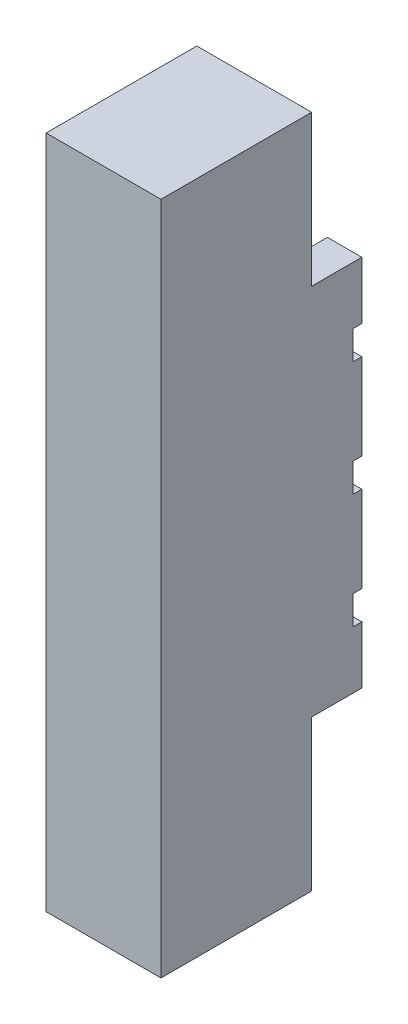
SolidWorks part; units mm, degrees
material "Alloy Steel"
ref_plane "Front Plane" through (0, 0, 0) normal (0, 0, 1) x (1, 0, 0)
ref_plane "Top Plane" through (0, 0, 0) normal (0, 1, 0) x (1, 0, 0)
ref_plane "Right Plane" through (0, 0, 0) normal (1, 0, 0) x (0, 0, -1)
sketch "Sketch1" plane through (0, 0, 0) normal (0, 1, 0) x (1, 0, 0)
  line L0 (0, 27.5) -> (0, 0) construction
  line L1 (-20, -35) -> (20, -35)
  line L2 (-20, -35) -> (-20, 35)
  line L3 (-20, 35) -> (20, 35)
  line L4 (20, -35) -> (20, 35)
  line L5 (-20, -35) -> (20, 35) construction
  line L6 (-20, 35) -> (20, -35) construction
  line L7 (-8, 35) -> (-8, 27.5)
  line L8 (-8, 27.5) -> (8, 27.5)
  line L9 (8, 27.5) -> (8, 35)
  point P0 (0, 0)
  dimension "D1" = 70
  dimension "D2" = 40
  dimension "D3" = 16
  dimension "D4" = 7.5
extrude "Boss-Extrude1" add sketch "Sketch1" along normal blind 130 contours L9 L8 L7 L3 L2 L1 L4
sketch "Sketch2" plane through (0, 0, -35) normal (0, 0, -1) x (-1, 0, 0)
  line L0 (0, 0) -> (0, 130) construction
  line L1 (8, 130) -> (-8, 130) construction
  line L2 (20, 65) -> (-20, 65) construction
  line L3 (-20, 130) -> (-20, 0) construction
  line L4 (20, 75) -> (-20, 75) construction
  line L5 (20, 85) -> (-20, 85) construction
  line L6 (20, 95) -> (-20, 95) construction
  line L7 (20, 105) -> (-20, 105) construction
  line L8 (20, 115) -> (-20, 115) construction
  line L9 (20, 55) -> (-20, 55) construction
  line L10 (20, 45) -> (-20, 45) construction
  line L11 (20, 35) -> (-20, 35) construction
  line L12 (20, 25) -> (-20, 25) construction
  line L13 (20, 15) -> (-20, 15) construction
  line L15 (20, 30) -> (-20, 30)
  line L16 (20, 30) -> (20, 20)
  line L17 (20, 20) -> (-20, 20)
  line L18 (-20, 30) -> (-20, 20)
  line L19 (20, 30) -> (-20, 20) construction
  line L20 (20, 20) -> (-20, 30) construction
  line L37 (20, 70) -> (-20, 70)
  line L38 (20, 70) -> (20, 60)
  line L39 (20, 60) -> (-20, 60)
  line L40 (-20, 70) -> (-20, 60)
  line L41 (20, 70) -> (-20, 60) construction
  line L42 (20, 60) -> (-20, 70) construction
  line L44 (20, 110) -> (-20, 110)
  line L45 (20, 110) -> (20, 100)
  line L46 (20, 100) -> (-20, 100)
  line L47 (-20, 110) -> (-20, 100)
  line L48 (20, 110) -> (-20, 100) construction
  line L49 (20, 100) -> (-20, 110) construction
  point P5 (0, 25)
  point P8 (0, 65)
  point P35 (0, 65)
  point P36 (0, 105)
  dimension "D3" = 10
  dimension "D4" = 40
  dimension "D5" = 10
  dimension "D6" = 10
  dimension "D7" = 10
  dimension "D8" = 40
  dimension "D9" = 40
  dimension "D10" = 10
  dimension "D1" = 6
  dimension "D2" = 6
extrude "Cut-Extrude1" cut sketch "Sketch2" against normal blind 3
sketch "Sketch3" plane through (0, 0, -32) normal (0, 0, -1) x (-1, 0, 0)
  line L0 (14, 20) -> (14, 110) construction
  line L1 (8, 20) -> (20, 20) construction
  line L3 (-14, 20) -> (-14, 110) construction
  line L4 (-20, 20) -> (-8, 20) construction
  line L6 (0, 0) -> (0, 130) construction
  line L7 (8, 130) -> (-8, 130) construction
  line L8 (-14, 20) -> (-14, 110) construction
  line L9 (20, 110) -> (8, 110) construction
  line L10 (-8, 110) -> (-20, 110) construction
  point P12 (14, 25)
  point P13 (14, 65)
  point P15 (14, 105)
  point P27 (-14, 105)
  point P28 (-14, 25)
  point P29 (-14, 65)
  dimension "D1" = 5
  dimension "D3" = 40
  dimension "D2" = 3
hole_wizard "M3 Tapped Hole1" positions "3DSketch2" profile "Sketch6" tap size "M3" standard "DIN"
sketch3d "3DSketch2"
  point P0 (-14, 25, -32)
  point P3 (14, 25, -32)
  point P12 (-14, 105, -32)
  point P15 (14, 105, -32)
  point P53 (-14, 65, -32)
  point P56 (14, 65, -32)
cosmetic thread "Cosmetic Thread1" parameters "D2"=3
cosmetic thread "Cosmetic Thread3" parameters "D2"=3
cosmetic thread "Cosmetic Thread4" parameters "D2"=3
cosmetic thread "Cosmetic Thread6" parameters "D2"=3
cosmetic thread "Cosmetic Thread7" parameters "D2"=3
cosmetic thread "Cosmetic Thread9" parameters "D2"=3
sketch "Sketch6" plane through (-14, 25, -32) normal (1, 0, 0) x (0, 1, 0)
  line L0 (0, 0) -> (0, 8.7511)
  line L1 (0, 8.7511) -> (1.25, 8)
  line L2 (1.25, 8) -> (1.25, 0)
  line L5 (1.25, 0) -> (0, 0)
  line L10 (0, 8.7511) -> (-1.25, 8) construction
  line L11 (0, -6.35) -> (0, 107.95) construction
  dimension "Tap Drill Dia." = 2.5
  dimension "Tap Drill Depth" = 8
  dimension "Drill Angle" = 118
sketch "Sketch7" plane through (0, 0, -27.5) normal (0, 0, -1) x (-1, 0, 0)
  line L0 (0, 0) -> (0, 130) construction
  line L1 (8, 0) -> (-8, 0) construction
  line L2 (8, 130) -> (-8, 130) construction
  line L3 (14, 25) -> (-14, 25) construction
  line L4 (-14, 65) -> (14, 65) construction
  line L5 (14, 105) -> (-14, 105) construction
  point P18 (0, 65)
  point P19 (0, 25)
  point P20 (0, 105)
hole_wizard "M3 Tapped Hole2" positions "3DSketch3" profile "Sketch8" tap size "M3" standard "DIN"
sketch3d "3DSketch3"
  point P0 (0, 25, -27.5)
  point P3 (0, 65, -27.5)
  point P6 (0, 105, -27.5)
cosmetic thread "Cosmetic Thread2" parameters "D2"=3
cosmetic thread "Cosmetic Thread5" parameters "D2"=3
cosmetic thread "Cosmetic Thread8" parameters "D2"=3
sketch "Sketch8" plane through (0, 25, -27.5) normal (1, 0, 0) x (0, 1, 0)
  line L0 (0, 0) -> (0, 8.7511)
  line L1 (0, 8.7511) -> (1.25, 8)
  line L2 (1.25, 8) -> (1.25, 0)
  line L5 (1.25, 0) -> (0, 0)
  line L10 (0, 8.7511) -> (-1.25, 8) construction
  line L11 (0, -6.35) -> (0, 107.95) construction
  dimension "Tap Drill Dia." = 2.5
  dimension "Tap Drill Depth" = 8
  dimension "Drill Angle" = 118
sketch "Sketch9" plane through (-20, 0, 0) normal (-1, 0, 0) x (0, 0, 1)
  line L1 (-17.5, -52.5) -> (-17.5, 0)
  line L2 (35, 0) -> (-35, 0) construction
  line L3 (35, 0) -> (-17.5, 0)
  line L4 (35, 65) -> (-32, 65) construction
  line L5 (35, 130) -> (35, 0) construction
  line L6 (-32, 60) -> (-32, 70) construction
  line L7 (35, 130) -> (-17.5, 130)
  line L8 (-17.5, 182.5) -> (-17.5, 130)
  line L10 (35, 0) -> (35, -52.5)
  line L11 (35, -52.5) -> (-17.5, -52.5)
  line L12 (-17.5, 182.5) -> (35, 182.5)
  line L13 (35, 182.5) -> (35, 130)
  dimension "D2" = 10
extrude "Boss-Extrude2" add sketch "Sketch9" against normal up to surface (40 mm away) up to face at (20, 65, -25.125)
equation "\"D8@Sketch2\"=\"D4@Sketch2\""
equation "\"D7@Sketch2\"=\"D3@Sketch2\""
equation "\"D9@Sketch2\"=\"D8@Sketch2\""
equation "\"D10@Sketch2\"=\"D7@Sketch2\""
